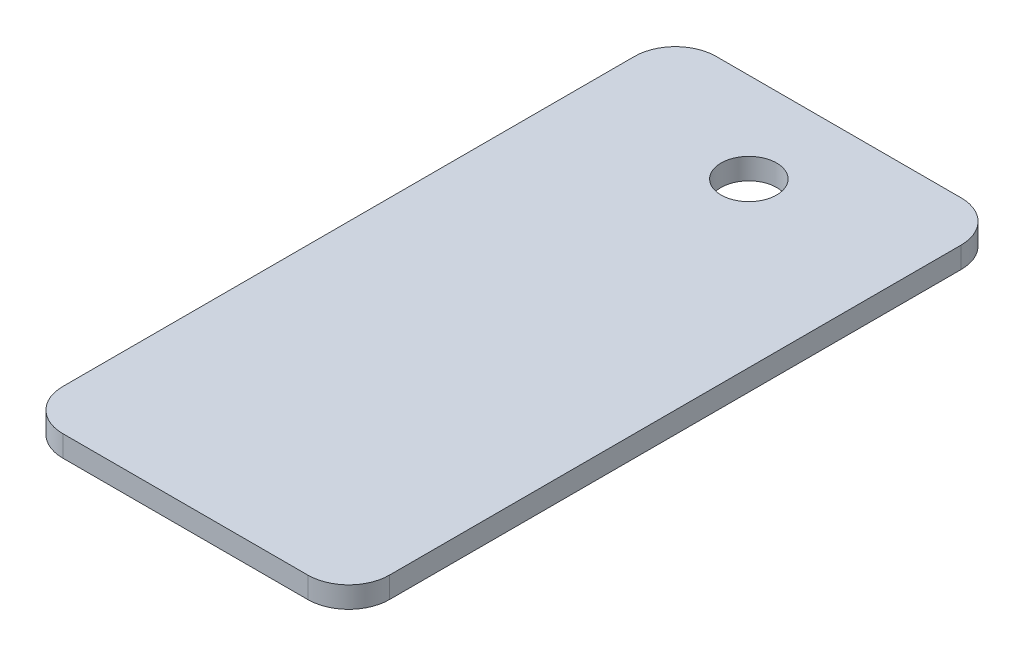
SolidWorks part; units mm, degrees
ref_plane "Front Plane" through (0, 0, 0) normal (0, 0, 1) x (1, 0, 0)
ref_plane "Top Plane" through (0, 0, 0) normal (0, 1, 0) x (1, 0, 0)
ref_plane "Right Plane" through (0, 0, 0) normal (1, 0, 0) x (0, 0, -1)
sketch "Sketch1" plane through (0, 0, 0) normal (0, 1, 0) x (1, 0, 0)
  line L1 (0, 0) -> (20, 0)
  line L2 (0, 0) -> (0, -40)
  line L3 (0, -40) -> (20, -40)
  line L4 (20, 0) -> (20, -40)
  dimension "D1" = 20
  dimension "D2" = 40
extrude "Boss-Extrude1" add sketch "Sketch1" along normal blind 1.3
sketch "Sketch2" plane through (0, 1.3, 0) normal (0, 1, 0) x (1, 0, 0)
  line L1 (20, 0) -> (0, 0) construction
  line L2 (10, 0) -> (10, -18.3716) construction
  point P0 (10, -5.5)
  point P8 (0, 0)
  dimension "D2" = 5.5
hole_wizard "M3 Clearance Hole1" positions "Sketch2" profile "Sketch3" hole size "M3" standard "ANSI Metric" end condition up to next
sketch "Sketch3" plane through (10, 1.3, 5.5) normal (1, 0, 0) x (0, 0, 1)
  line L0 (0, 0) -> (0, 1.3)
  line L1 (0, 1.3) -> (1.7, 1.3)
  line L2 (1.7, 1.3) -> (1.7, 0)
  line L5 (1.7, 0) -> (0, 0)
  line L11 (0, -6.35) -> (0, 107.95) construction
  dimension "Thru Hole Dia." = 3.4
  dimension "Thru Hole Depth" = 1.3
fillet "Fillet1" radius 2.5 4 edges at (20, 0.65, 40) (0, 0.65, 40) (0, 0.65, 0) (20, 0.65, 0)
